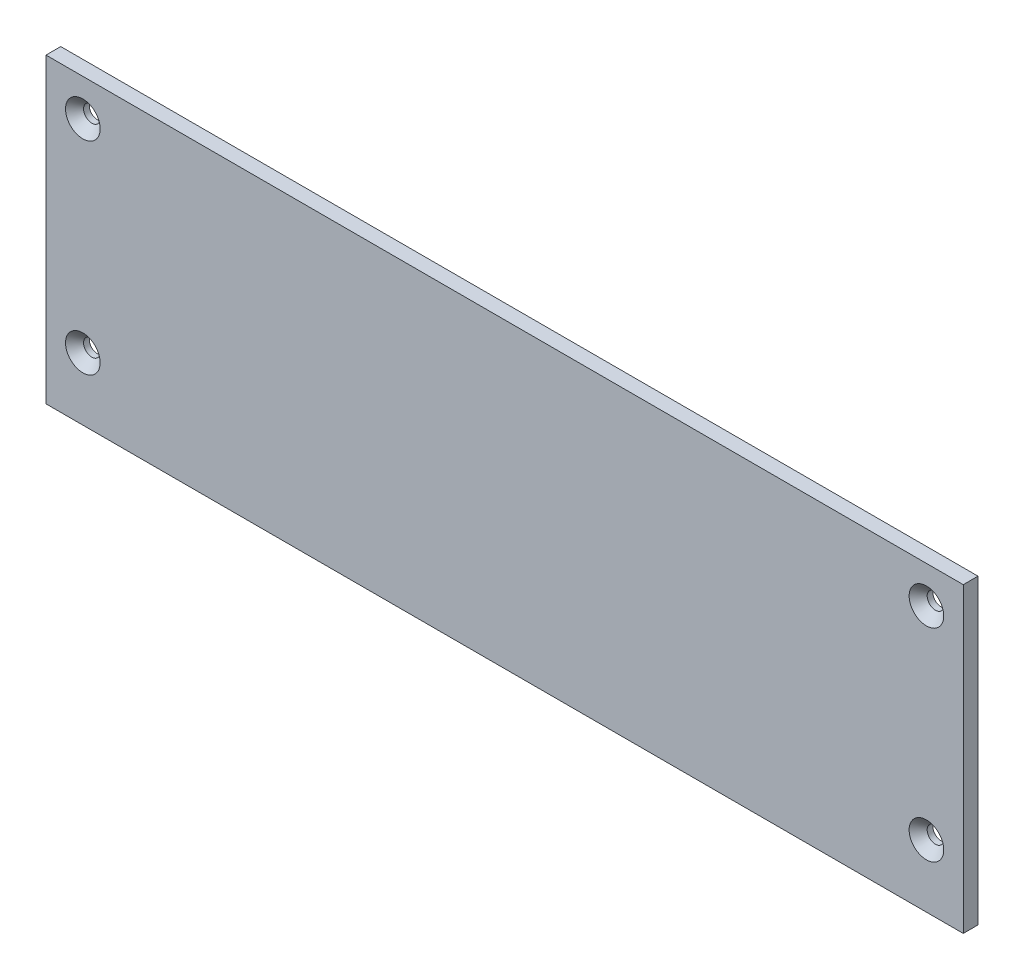
SolidWorks part; units mm, degrees
ref_plane "Plan de face" through (0, 0, 0) normal (0, 0, 1) x (1, 0, 0)
ref_plane "Plan de dessus" through (0, 0, 0) normal (0, 1, 0) x (1, 0, 0)
ref_plane "Plan de droite" through (0, 0, 0) normal (1, 0, 0) x (0, 0, -1)
sketch "Esquisse1" plane through (0, 0, 0) normal (0, 0, 1) x (1, 0, 0)
  line L0 (-124.5, 41) -> (-124.5, -41)
  line L1 (-124.5, -41) -> (124.5, -41)
  line L2 (0, -2.2) -> (0, 2.2) construction
  line L3 (124.5, 41) -> (124.5, -41)
  line L4 (2.2, 0) -> (-2.2, 0) construction
  line L5 (-124.5, 41) -> (124.5, 41)
  dimension "D1" = 82
  dimension "D2" = 249
extrude "Boss.-Extru.1" add sketch "Esquisse1" along normal blind 4
sketch "Esquisse2" plane through (0, 0, 4) normal (0, 0, 1) x (1, 0, 0)
  line L0 (-114.5, 41) -> (-114.5, 31) construction
  line L1 (124.5, 41) -> (-124.5, 41) construction
  line L2 (-114.5, 31) -> (-124.5, 31) construction
  line L3 (-124.5, 41) -> (-124.5, -41) construction
  line L4 (-124.5, -24) -> (-114.5, -24) construction
  line L5 (-114.5, -24) -> (-114.5, -41) construction
  line L6 (-124.5, -41) -> (124.5, -41) construction
  line L8 (0, -2.2) -> (0, 2.2) construction
  point P1 (-114.5, 31)
  point P8 (-114.5, -24)
  point P15 (114.5, -24)
  point P16 (114.5, 31)
  point P19 (-114.5, 31)
  point P22 (-114.5, -24)
  dimension "D1" = 10
  dimension "D2" = 10
  dimension "D3" = 17
hole_wizard "Fraisage pour vis à tête fraisée M42" positions "Esquisse2" profile "Esquisse6" countersink size "M4" standard "Ansi Metric" end condition through all
sketch "Esquisse6" plane through (-114.5, -24, 4) normal (1, 0, 0) x (0, -1, 0)
  line L0 (0, 0) -> (0, 4)
  line L1 (0, 4) -> (2.25, 4)
  line L2 (2.25, 4) -> (2.25, 2.45)
  line L3 (2.25, 2.45) -> (4.7, 0)
  line L5 (4.7, 0) -> (0, 0)
  line L6 (-2.25, 2.45) -> (-4.7, 0) construction
  line L11 (0, -6.35) -> (0, 107.95) construction
  dimension "Diamètre du perçage jusqu'au prochain" = 4.5
  dimension "Profondeur du perçage jusqu'au prochain" = 4
  dimension "Diamètre du fraisage entrant" = 9.4
  dimension "Angle du fraisage entrant" = 90
